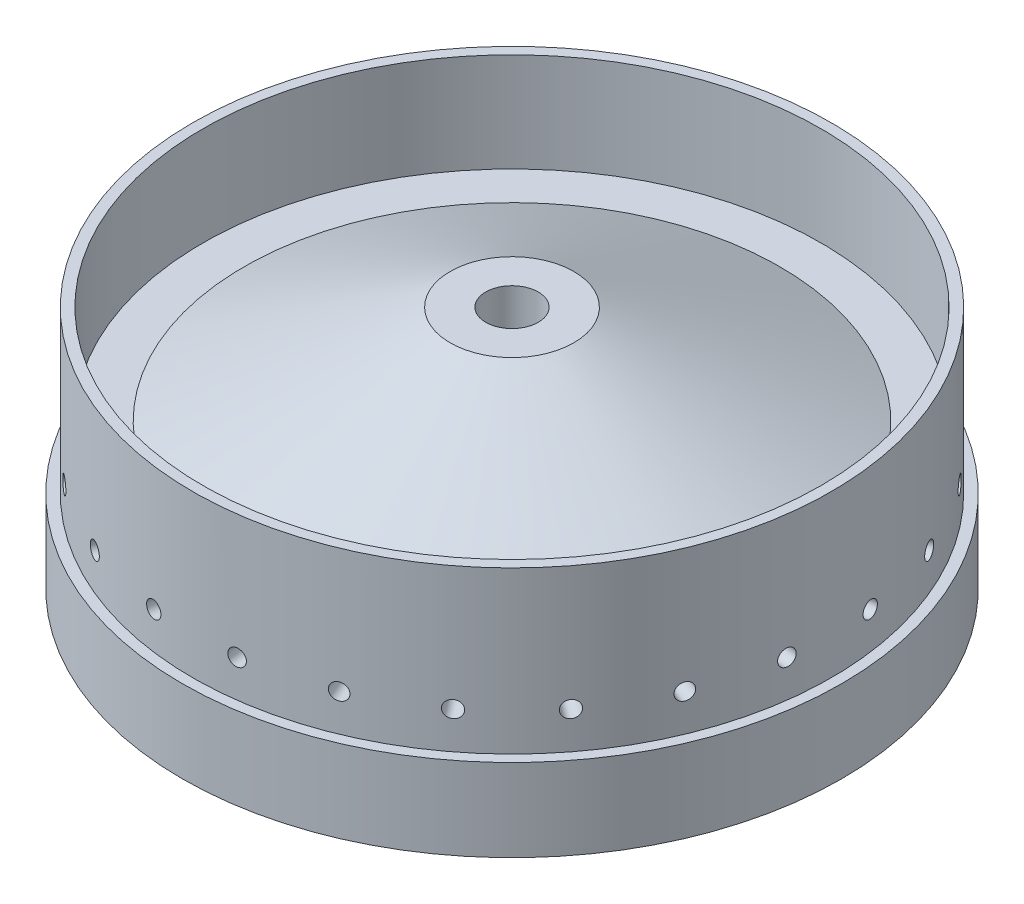
SolidWorks part; units mm, degrees
material "6061-T6 (SS)"
ref_plane "Front Plane" through (0, 0, 0) normal (0, 0, 1) x (1, 0, 0)
ref_plane "Top Plane" through (0, 0, 0) normal (0, 1, 0) x (1, 0, 0)
ref_plane "Right Plane" through (0, 0, 0) normal (1, 0, 0) x (0, 0, -1)
ref_plane "Plane1" through (0, 0, -75.0887) normal (0, 0, 1) x (1, 0, 0)
sketch "Sketch1" plane through (0, 0, 0) normal (0, 1, 0) x (1, 0, 0)
  line L1 (95.25, 0) -> (101.6, 0)
  line L2 (0, 0) -> (0, 61.9125) construction
  line L4 (101.6, 59.4931) -> (101.6, 0)
  line L6 (101.6, 59.4931) -> (8.0962, 59.4931) construction
  line L8 (0, 75.0887) -> (101.6, 75.0887)
  line L9 (101.6, 75.0887) -> (101.6, 59.4931)
  line L10 (8.0962, 0) -> (8.0962, 75.0887)
  line L11 (8.0962, 75.0887) -> (-8.0962, 75.0887)
  line L12 (-8.0962, 75.0887) -> (-8.0962, 0)
  line L13 (-8.0962, 0) -> (8.0962, 0)
  line L14 (8.0962, 59.4931) -> (0, 59.4931) construction
  line L15 (19.05, 75.0887) -> (82.55, 44.6088)
  line L16 (82.55, 44.6088) -> (95.25, 44.6088)
  line L17 (95.25, 44.6088) -> (95.25, 75.0887)
  ellipse E0 centre (0, 0) end of major axis (-95.25, 0) minor radius 59.4931
  point P18 (19.05, 75.0887)
  dimension "D4" = 15.5956
  dimension "D6" = 16.1925
  dimension "D7" = 6.35
  dimension "D8" = 30.48
  dimension "D9" = 12.7
  dimension "D10" = 19.05
  dimension "D2" = 101.6
  dimension "D3" = 75.0887
revolve "Revolve1" add sketch "Sketch1" angle 360 about L2
sketch "Sketch3" plane through (0, 0, 0) normal (0, 0, -1) x (-1, 0, 0)
  circle A0 centre (0, 0) radius 101.6
  circle A1 centre (0, 0) radius 98.425
  dimension "D1" = 203.2
  dimension "D2" = 3.175
extrude "Cut-Extrude2" cut sketch "Sketch3" along normal through all from offset 25.4
hole_wizard "1/4-20 Tapped Hole1" positions "3DSketch1" profile "Sketch10" tap size "1/4-20" standard "ANSI Inch"
sketch3d "3DSketch1"
  line L0 (97.583, 12.847, -36.83) -> (97.583, 12.847, 0) construction
  line L1 (97.583, 12.847, 0) -> (0, 0, 0) construction
  line L2 (0, 0, 0) -> (101.6, 0, 0) construction
  circle A0 centre (0, 0, 0) radius 101.6 construction
  point P0 (97.583, 12.847, -36.83)
  point P12 (0, 0, 101.6)
  dimension "D1" = 36.83
  dimension "D2" = 7.5
sketch "Sketch10" plane through (97.583, 12.847, -36.83) normal (0, 0, 1) x (-0.1305, 0.9914, 0)
  line L0 (0, 0) -> (0, 14.2338)
  line L1 (0, 14.2338) -> (2.5527, 12.7)
  line L2 (2.5527, 12.7) -> (2.5527, 0)
  line L5 (2.5527, 0) -> (0, 0)
  line L10 (0, 14.2338) -> (-2.5527, 12.7) construction
  line L11 (0, -6.35) -> (0, 107.95) construction
  dimension "Tap Drill Dia." = 5.1054
  dimension "Tap Drill Depth" = 12.7
  dimension "Drill Angle" = 118
cosmetic thread "Hole Thread2" parameters "D1"=12.7, "D2"=6.35
pattern_circular "CirPattern1" count 24 over 360 about axis through (0, 0, 0) along (0, 0, 1) of "1/4-20 Tapped Hole1"
sketch "Sketch13" plane through (0, 0, 0) normal (0, 0, 1) x (1, 0, 0)
  line L0 (-67.9108, -66.7883) -> (66.7883, 67.9108)
  line L1 (-66.7883, -67.9108) -> (67.9108, 66.7883)
  line L2 (0, 0) -> (0, -28.3739) construction
  circle A4 centre (0, 0) radius 95.25 construction
  arc A5 (-67.9108, -66.7883) -> (-66.7883, -67.9108) centre (0, 0) ccw
  arc A6 (66.7883, 67.9108) -> (67.9108, 66.7883) centre (0, 0) cw
  dimension "D1" = 1.5875
  dimension "D2" = 135
sketch "Sketch14" plane through (0, 0, -75.0888) normal (0, 0, -1) x (-1, 0, 0)
  circle A0 centre (0, 0) radius 8.0962
  circle A1 centre (0, 0) radius 8.0962 construction
move or copy body "Body-Move/Copy1" bodies to move or copy 120 copy no rotation origin (0, 0, -37.5444) rotation axis (1, 0, 0) rotation angle 90
equation "\"D7@Sketch1\"= .25"
equation "\"D1@Plane1\"= \"D3@Sketch1\""
